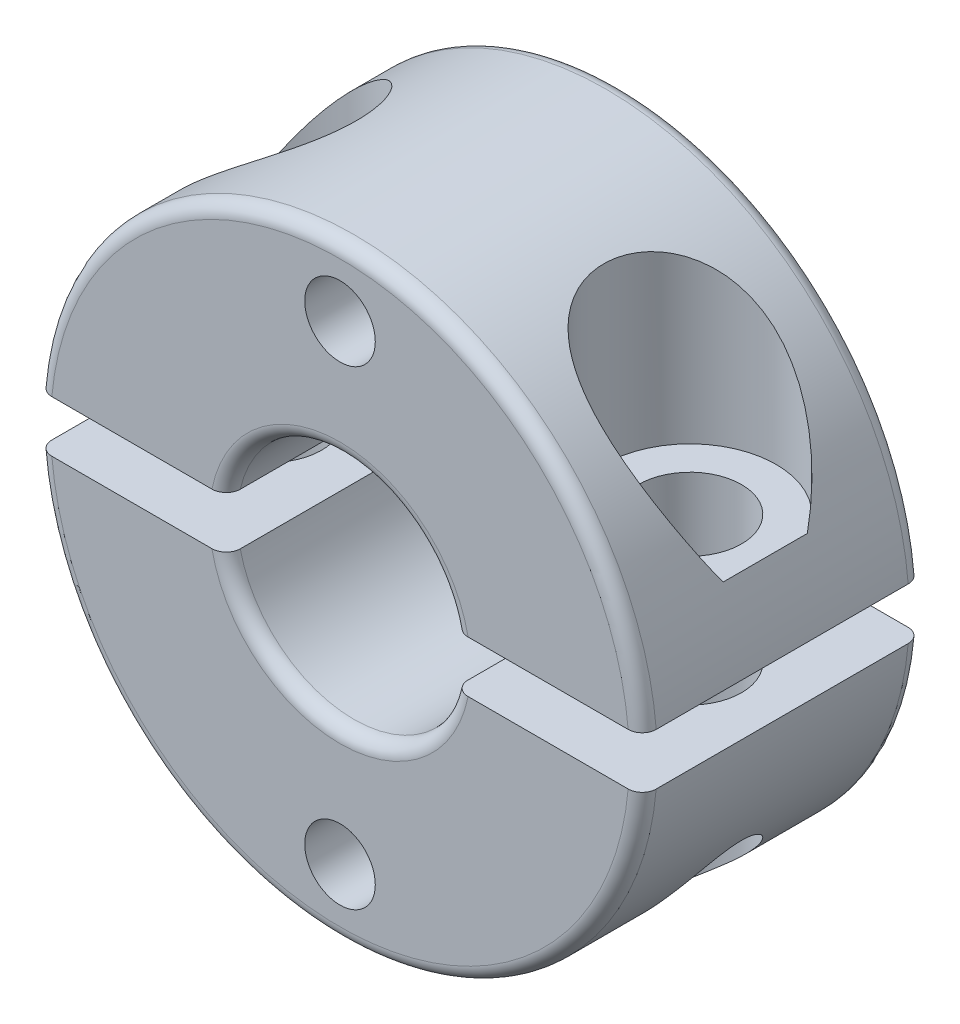
SolidWorks part; units mm, degrees
material "Nylon 6/10"
ref_plane "Front Plane" through (0, 0, 0) normal (0, 0, 1) x (1, 0, 0)
ref_plane "Top Plane" through (0, 0, 0) normal (0, 1, 0) x (1, 0, 0)
ref_plane "Right Plane" through (0, 0, 0) normal (1, 0, 0) x (0, 0, -1)
sketch "Sketch1" plane through (0, 0, 0) normal (0, 0, 1) x (1, 0, 0)
  line L0 (-10.3187, 0) -> (-3.9688, 0) construction
  line L1 (-10.2814, 0.8771) -> (-3.8706, 0.8771)
  line L2 (-10.2814, -0.8771) -> (-3.8706, -0.8771)
  line L3 (3.8706, 0.8771) -> (10.2814, 0.8771)
  line L4 (3.8706, -0.8771) -> (10.2814, -0.8771)
  line L5 (0, 0) -> (0, 10.3187) construction
  line L6 (-7.1438, 0) -> (-7.1438, 0.8771) construction
  line L7 (-7.1438, 0) -> (-7.1438, -0.8771) construction
  line L8 (7.076, 0.8771) -> (7.076, -0.8771) construction
  circle A0 centre (0, 0) radius 10.3187 construction
  circle A1 centre (0, 0) radius 3.9688 construction
  arc A4 (-3.8706, -0.8771) -> (3.8706, -0.8771) centre (0, 0) ccw
  arc A5 (-10.2814, -0.8771) -> (10.2814, -0.8771) centre (0, 0) ccw
  arc A6 (3.8706, 0.8771) -> (-3.8706, 0.8771) centre (0, 0) ccw
  arc A7 (10.2814, 0.8771) -> (-10.2814, 0.8771) centre (0, 0) ccw
  point P4 (10.3187, 0)
  point P14 (-10.3187, 0)
  point P19 (-3.9688, 0)
  point P21 (3.9688, 0)
  dimension "D1" = 14.2198
  dimension "Bore Dia" = 7.9375
  dimension "OD" = 20.6375
  dimension "Separation" = 1.7542
extrude "Extrude1" add sketch "Sketch1" along normal mid plane 9.525
fillet "Fillet1" radius 0.4763 4 edges at (0, 3.9688, 4.7625) (0, 3.9688, -4.7625) (0, 10.3188, -4.7625) (0, 10.3188, 4.7625)
fillet "Fillet2" radius 0.4763 4 edges at (0, -10.3187, 4.7625) (0, -3.9688, 4.7625) (0, -3.9688, -4.7625) (0, -10.3187, -4.7625)
sketch "Sketch2" plane through (0, 0, 0) normal (0, 1, 0) x (1, 0, 0)
  line L0 (0, 4.7625) -> (0, -4.7625) construction
  line L3 (0, 0) -> (-3.9688, 0) construction
  line L4 (-3.9688, 0) -> (-10.3187, 0) construction
  line L7 (-7.1438, 4.7625) -> (-7.1438, -4.7625) construction
  line L8 (-7.3343, 4.7625) -> (-6.9533, 4.7625)
  line L9 (-9.8033, -4.7625) -> (9.8033, -4.7625) construction
  line L10 (-10.3187, 0) -> (-3.9688, 0) construction
  line L11 (9.8033, 4.7625) -> (-9.8033, 4.7625) construction
  arc A0 (-7.3343, 4.7625) -> (-6.9533, 4.7625) centre (-7.1438, 4.7625) ccw
  point P16 (-7.1438, 0)
  dimension "D2" = 0.1905
revolve "Cut-Revolve1" cut sketch "Sketch2" angle 360 about L0
sketch "Sketch3" plane through (0, 0, 0) normal (0, 0, 1) x (1, 0, 0)
  line L0 (-7.1438, 10.3188) -> (-4.21, 10.3187)
  line L1 (-4.21, 10.3187) -> (-4.21, 3.506)
  line L2 (-4.21, 3.506) -> (-5.3912, 3.506)
  line L3 (-5.3912, 3.506) -> (-5.3911, -10.3187)
  line L4 (-5.3911, -10.3187) -> (-7.1438, -10.3188)
  line L5 (-7.1438, -10.3188) -> (-7.1438, 10.3188)
  line L7 (-7.1438, 10.3188) -> (-7.1438, 13.2525) construction
  line L8 (-4.21, 10.3187) -> (0, 10.3187) construction
  line L9 (0, -10.3187) -> (-5.3911, -10.3187) construction
  line L10 (-10.3187, 0) -> (-3.9688, 0) construction
  line L11 (-10.2814, 0.8771) -> (-3.8706, 0.8771) construction
  line L12 (0, 0) -> (0, -10.3187) construction
  line L13 (-7.1438, 0) -> (-7.1438, -0.8771) construction
  circle A0 centre (0, 0) radius 10.3187 construction
  circle A2 centre (0, 0) radius 3.9688 construction
  arc A4 (-10.2814, -0.8771) -> (10.2814, -0.8771) centre (0, 0) ccw construction
  dimension "D3" = 2.6289
  dimension "D1" = 5.8674
revolve "Cut-Revolve2" cut sketch "Sketch3" angle 360 about L5
mirror "Mirror1" about plane through (0, 0, 0) normal (1, 0, 0) of "Cut-Revolve2"
sketch "Sketch8" plane through (0, 3.506, 0) normal (0, 1, 0) x (1, 0, 0)
  circle A0 centre (7.1438, 0) radius 1.7526 construction
  circle A1 centre (7.1438, 0) radius 1.7526
extrude "Cut-Extrude3" cut sketch "Sketch8" against normal through all
hole_wizard "M2 Clearance Hole1" positions "Sketch9" profile "Sketch10" hole size "M2" standard "ANSI Metric" end condition through all
sketch "Sketch9" plane through (0, 0, -4.7625) normal (0, 0, -1) x (-1, 0, 0)
  circle A0 centre (0, 0) radius 8
  point P0 (0, 8)
  point P2 (0, -8)
  dimension "D1" = 8
sketch "Sketch10" plane through (0, 8, -4.7625) normal (1, 0, 0) x (0, 1, 0)
  line L0 (0, 0) -> (0, 9.5534)
  line L1 (0, 9.5534) -> (1.2, 9.5534)
  line L2 (1.2, 9.5534) -> (1.2, 0)
  line L5 (1.2, 0) -> (0, 0)
  line L11 (0, -6.35) -> (0, 107.95) construction
  dimension "Thru Hole Dia." = 2.4
  dimension "Thru Hole Depth" = 9.5534
equation "\"D1@Fillet1\" = \"Width@Extrude1\"*.05"
equation "\"D1@Fillet2\" = \"D1@Fillet1\""
equation "\"D3@Sketch3\" = \"Screw Dia@Sketch3\"*.750"
